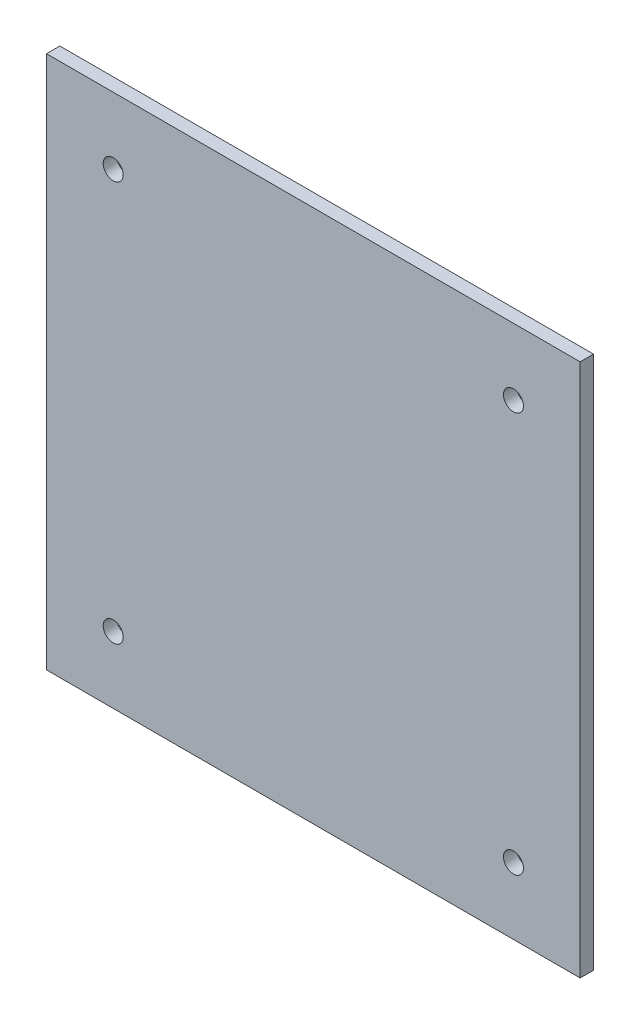
SolidWorks part; units mm, degrees
ref_plane "Front Plane" through (0, 0, 0) normal (0, 0, 1) x (1, 0, 0)
ref_plane "Top Plane" through (0, 0, 0) normal (0, 1, 0) x (1, 0, 0)
ref_plane "Right Plane" through (0, 0, 0) normal (1, 0, 0) x (0, 0, -1)
sketch "Sketch2" plane through (0, 0, 0) normal (0, 0, 1) x (1, 0, 0)
  line L0 (0, 0) -> (0, 80)
  line L1 (0, 80) -> (80, 80)
  line L2 (80, 80) -> (80, 0)
  line L3 (80, 0) -> (0, 0)
extrude "Boss-Extrude1" add sketch "Sketch2" along normal blind 2
sketch "Sketch3" plane through (0, 0, 0) normal (0, 0, -1) x (-1, 0, 0)
  line L0 (-70, 0) -> (-70, 80)
  line L5 (-80, 0) -> (0, 0)
  line L6 (-80, 0) -> (-80, 80)
  line L7 (-80, 80) -> (0, 80)
  line L8 (0, 0) -> (0, 80)
  line L9 (-70, 10) -> (-10, 10)
  line L10 (-10, 0) -> (-10, 80)
  line L11 (-70, 10) -> (-10, 10) construction
  line L12 (-70, 10) -> (-70, 70) construction
  line L14 (-80, 70) -> (0, 70)
  line L15 (-70, 70) -> (-10, 70)
  line L16 (-80, 10) -> (0, 10) construction
  circle A0 centre (-70, 10) radius 1.5
  circle A1 centre (-10, 10) radius 1.5
  circle A2 centre (-10, 70) radius 1.5
  circle A3 centre (-70, 70) radius 1.5
  dimension "D5" = 2
  dimension "D1" = 10
  dimension "D6" = 60
  dimension "D7" = 60
  dimension "D2" = 10
  dimension "D3" = 10
  dimension "D4" = 10
extrude "Cut-Extrude1" cut sketch "Sketch3" against normal blind 10 contours A0 | A3 | A2 | A1
